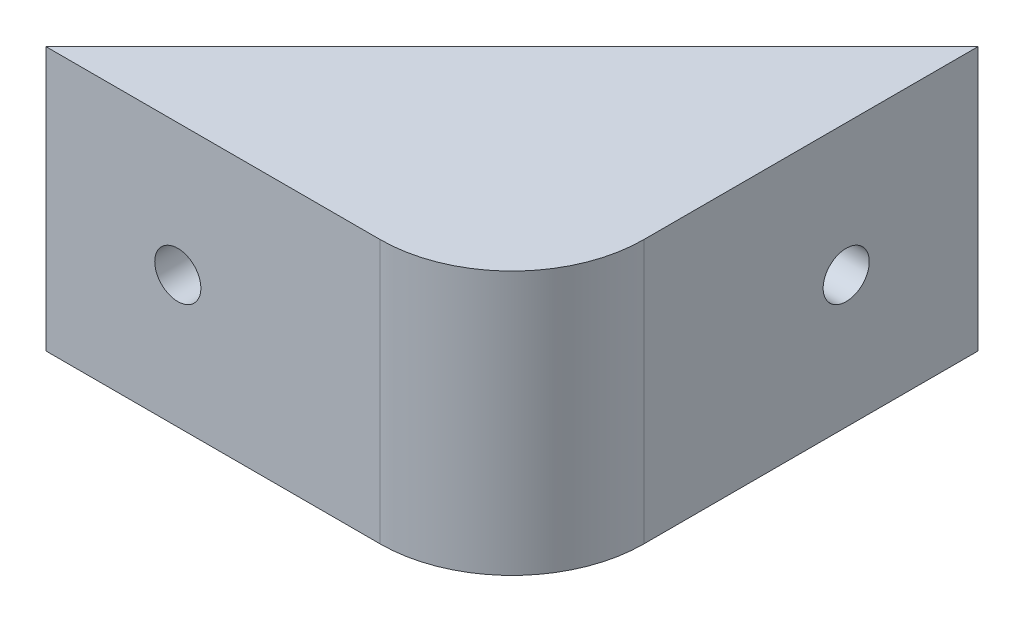
SolidWorks part; units mm, degrees
material "ABS"
ref_plane "Front Plane" through (0, 0, 0) normal (0, 0, 1) x (1, 0, 0)
ref_plane "Top Plane" through (0, 0, 0) normal (0, 1, 0) x (1, 0, 0)
ref_plane "Right Plane" through (0, 0, 0) normal (1, 0, 0) x (0, 0, -1)
sketch "Sketch1" plane through (0, 0, 0) normal (0, 1, 0) x (1, 0, 0)
  line L0 (0, 0) -> (0, 35.3553)
  line L1 (0, 35.3553) -> (-35.3553, 0)
  line L2 (-35.3553, 0) -> (0, 0)
  dimension "D1" = 50
  dimension "D2" = 45
extrude "Boss-Extrude1" add sketch "Sketch1" along normal mid plane 20
fillet "Fillet1" radius 10 1 edges at (0, 0, 0)
sketch "Sketch5" plane through (0, 0, 0) normal (0, 0, 1) x (1, 0, 0)
  line L0 (-10, -10) -> (-10, 10) construction
  line L1 (-35.3553, 7.5) -> (-10, 7.5)
  line L2 (-35.3553, 7.5) -> (-35.3553, -7.5)
  line L3 (-35.3553, -7.5) -> (-10, -7.5)
  line L4 (-10, 7.5) -> (-10, -7.5)
  line L5 (-35.3553, 10) -> (-10, 10) construction
  line L6 (-35.3553, -10) -> (-10, -10) construction
  line L7 (-35.3553, 10) -> (-35.3553, -10) construction
  dimension "D1" = 2.5
  dimension "D2" = 2.5
extrude "Cut-Extrude1" cut sketch "Sketch5" against normal through all from offset 5 offset against normal yes
sketch "Sketch6" plane through (0, 0, 0) normal (1, 0, 0) x (0, 0, -1)
  line L1 (10, 7.5) -> (35.3553, 7.5)
  line L2 (10, 7.5) -> (10, -7.5)
  line L3 (10, -7.5) -> (35.3553, -7.5)
  line L4 (35.3553, 7.5) -> (35.3553, -7.5)
  line L6 (10, 10) -> (10, -10) construction
  line L7 (10, -10) -> (35.3553, -10) construction
  line L8 (10, 10) -> (35.3553, 10) construction
  line L9 (35.3553, 10) -> (35.3553, -10) construction
  dimension "D1" = 2.5
  dimension "D2" = 2.5
extrude "Cut-Extrude3" cut sketch "Sketch6" against normal through all from offset 5 offset against normal yes
sketch "Sketch8" plane through (0, 0, -10) normal (0, 0, -1) x (-1, 0, 0)
  line L4 (10, 7.5) -> (5, 7.5)
  line L5 (5, 7.5) -> (5, -7.5)
  line L6 (5, -7.5) -> (10, -7.5)
  line L7 (10, -7.5) -> (10, 7.5)
  line L8 (10, 7.5) -> (5, 7.5)
  line L9 (5, 7.5) -> (5, -7.5)
  line L10 (5, -7.5) -> (10, -7.5)
  line L11 (10, -7.5) -> (10, 7.5)
  dimension "D1" = 0
revolve "Cut-Revolve2" cut sketch "Sketch8" angle 360 about L11
sketch "Sketch9" plane through (-5, 0, 0) normal (-1, 0, 0) x (0, 0, 1)
  line L0 (-35.3553, -10) -> (0, -10) construction
  line L1 (-35.3553, 10) -> (-35.3553, -10) construction
  circle A0 centre (-25.3553, 0) radius 1.75
  dimension "D2" = 3.5
  dimension "D1" = 10
  dimension "D3" = 10
extrude "Cut-Extrude4" cut sketch "Sketch9" against normal through all
sketch "Sketch10" plane through (0, 0, -5) normal (0, 0, -1) x (-1, 0, 0)
  line L0 (0, -10) -> (35.3553, -10) construction
  line L1 (35.3553, 10) -> (35.3553, -10) construction
  circle A0 centre (25.3553, 0) radius 1.75
  dimension "D3" = 3.5
  dimension "D1" = 10
  dimension "D2" = 10
extrude "Cut-Extrude5" cut sketch "Sketch10" against normal through all
